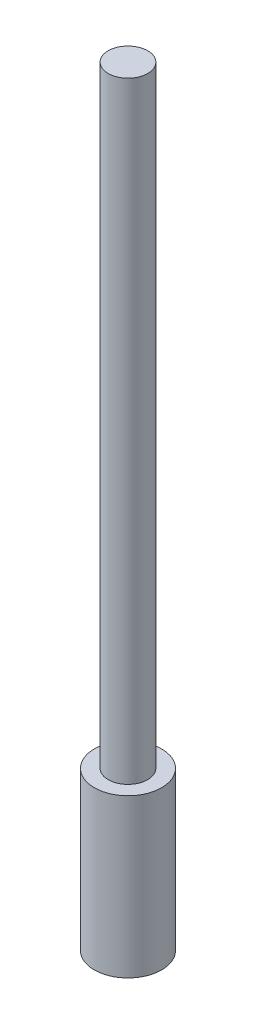
SolidWorks part; units mm, degrees
ref_plane "Front Plane" through (0, 0, 0) normal (0, 0, 1) x (1, 0, 0)
ref_plane "Top Plane" through (0, 0, 0) normal (0, 1, 0) x (1, 0, 0)
ref_plane "Right Plane" through (0, 0, 0) normal (1, 0, 0) x (0, 0, -1)
sketch "Sketch1" plane through (0, 0, 0) normal (0, 1, 0) x (1, 0, 0)
  circle A0 centre (0, 0) radius 8.525
extrude "Boss-Extrude1" add sketch "Sketch1" along normal blind 40
sketch "Sketch2" plane through (0, 40, 0) normal (0, 1, 0) x (1, 0, 0)
  circle A0 centre (0, 0) radius 5
extrude "Boss-Extrude2" add sketch "Sketch2" along normal blind 155
